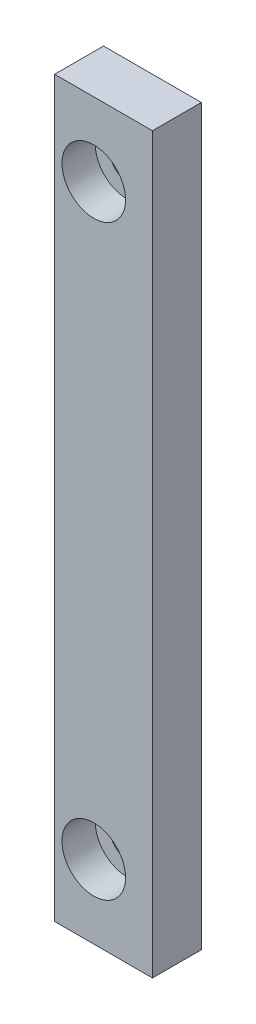
SolidWorks part; units mm, degrees
ref_plane "前视基准面" through (0, 0, 0) normal (0, 0, 1) x (1, 0, 0)
ref_plane "上视基准面" through (0, 0, 0) normal (0, 1, 0) x (1, 0, 0)
ref_plane "右视基准面" through (0, 0, 0) normal (1, 0, 0) x (0, 0, -1)
sketch "草图1" plane through (0, 0, 0) normal (0, 0, 1) x (1, 0, 0)
  line L1 (0, 0) -> (10, 0)
  line L2 (0, 0) -> (0, 75)
  line L3 (0, 75) -> (10, 75)
  line L4 (10, 0) -> (10, 75)
  dimension "D1" = 75
  dimension "D2" = 10
extrude "凸台-拉伸1" add sketch "草图1" along normal blind 5
hole_wizard "M3 六角凹头螺钉的柱形沉头孔1" positions "草图2" profile "草图3" counterbore size "M3" standard "ISO"
sketch "草图2" plane through (0, 0, 5) normal (0, 0, 1) x (1, 0, 0)
  line L0 (0, 37.5) -> (10, 37.5) construction
  line L1 (0, 75) -> (0, 0) construction
  line L2 (10, 0) -> (10, 75) construction
  line L3 (10, 37.5) -> (5, 37.5) construction
  line L4 (5, 37.5) -> (5, -18.9158) construction
  point P0 (4, 67.5)
  point P15 (4, 7.5)
  dimension "D1" = 4
  dimension "D2" = 60
sketch "草图3" plane through (4, 67.5, 5) normal (1, 0, 0) x (0, -1, 0)
  line L0 (0, 0) -> (0, 11.1215)
  line L1 (0, 11.1215) -> (1.7, 10.1)
  line L2 (1.7, 10.1) -> (1.7, 3.4)
  line L3 (1.7, 3.4) -> (3.25, 3.4)
  line L4 (3.25, 3.4) -> (3.25, 0)
  line L5 (3.25, 0) -> (0, 0)
  line L10 (0, 11.1215) -> (-1.7, 10.1) construction
  line L11 (0, -6.35) -> (0, 107.95) construction
  dimension "孔直径" = 3.4
  dimension "孔深度" = 10.1
  dimension "柱形沉头孔直径" = 6.5
  dimension "柱形沉头孔深度" = 3.4
  dimension "导头角度" = 118
